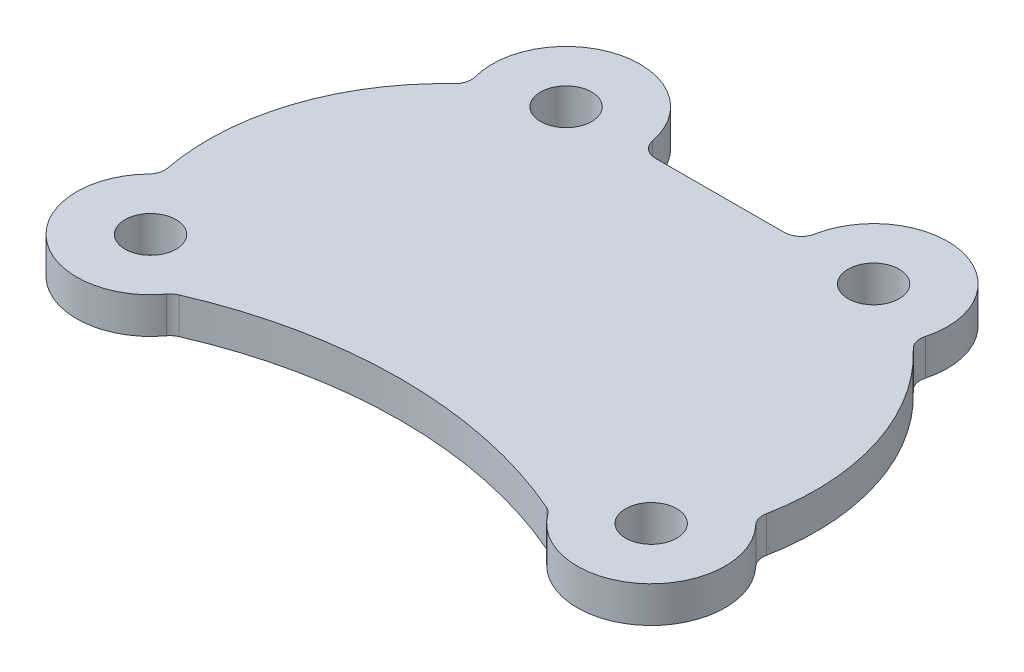
SolidWorks part; units mm, degrees
ref_plane "Front" through (0, 0, 0) normal (0, 0, 1) x (1, 0, 0)
ref_plane "Top" through (0, 0, 0) normal (0, 1, 0) x (1, 0, 0)
ref_plane "Right" through (0, 0, 0) normal (1, 0, 0) x (0, 0, -1)
sketch "Sketch1" plane through (0, 0, 0) normal (0, 1, 0) x (1, 0, 0)
  line L0 (0, 0) -> (88, 0) construction
  line L1 (88, 0) -> (71.0909, 56.003) construction
  line L2 (17.0909, 55.9477) -> (71.0909, 56.003) construction
  line L3 (17.0909, 55.9477) -> (0, 0) construction
  line L4 (71.0909, 56.003) -> (0, 0) construction
  line L5 (32.8121, 55.9531) -> (55.3796, 55.9976)
  circle A0 centre (17.0909, 55.9477) radius 4.5
  circle A1 centre (71.0909, 56.003) radius 4.5
  circle A2 centre (0, 0) radius 4.5
  circle A3 centre (88, 0) radius 4.5
  arc A4 (29.8595, 58.3896) -> (4.5425, 52.5513) centre (17.0909, 55.9477) ccw
  arc A5 (83.6309, 52.5753) -> (58.3206, 58.4361) centre (71.0909, 56.003) ccw
  arc A6 (-9.386, 8.9946) -> (10.4755, -7.6983) centre (0, 0) ccw
  arc A7 (77.5245, -7.6983) -> (97.4133, 8.9661) centre (88, 0) ccw
  arc A8 (84.4636, 49.6044) -> (96.6413, 11.6107) centre (56.044, 19.5469) cw
  arc A9 (3.7004, 49.5808) -> (-8.6057, 11.6355) centre (32.0193, 19.4284) ccw
  arc A10 (11.6959, -6.724) -> (76.3041, -6.724) centre (44, -80.9615) cw
  arc A11 (32.8121, 55.9531) -> (29.8595, 58.3896) centre (32.8061, 58.9531) cw
  arc A12 (55.3796, 55.9976) -> (58.3206, 58.4361) centre (55.3737, 58.9976) ccw
  arc A13 (3.7004, 49.5808) -> (4.5425, 52.5513) centre (1.6467, 51.7675) ccw
  arc A14 (-9.386, 8.9946) -> (-8.6057, 11.6355) centre (-11.552, 11.0703) ccw
  arc A15 (11.6959, -6.724) -> (10.4755, -7.6983) centre (12.8929, -9.4748) ccw
  arc A16 (77.5245, -7.6983) -> (76.3041, -6.724) centre (75.1071, -9.4748) ccw
  arc A17 (96.6413, 11.6107) -> (97.4133, 8.9661) centre (99.5856, 11.0352) ccw
  arc A18 (83.6309, 52.5753) -> (84.4636, 49.6044) centre (86.5247, 51.7842) ccw
  point P19 (30.0909, 55.9477)
  dimension "D6" = 3
  dimension "D1" = 88
  dimension "D2" = 58.5
  dimension "D3" = 58.5
  dimension "D4" = 90.5
  dimension "D5" = 54
extrude "Extrude1" add sketch "Sketch1" along normal blind 6.35
